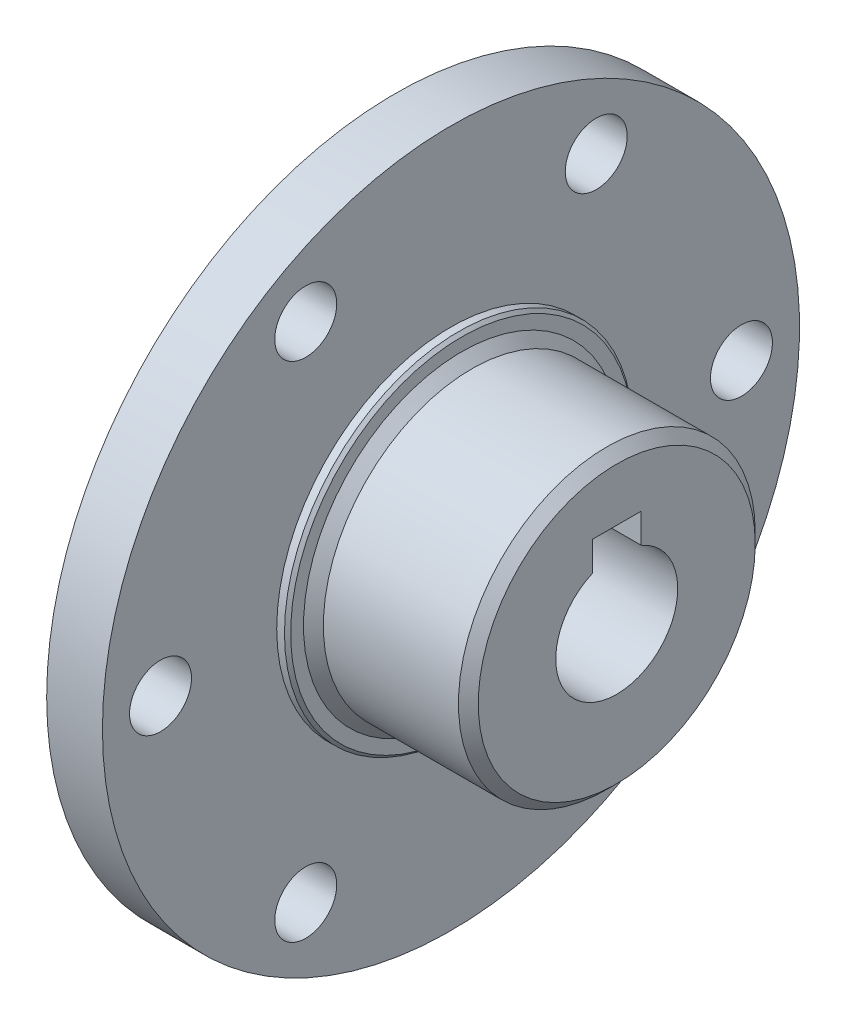
SolidWorks part; units mm, degrees
ref_plane "Front Plane" through (0, 0, 0) normal (0, 0, 1) x (1, 0, 0)
ref_plane "Top Plane" through (0, 0, 0) normal (0, 1, 0) x (1, 0, 0)
ref_plane "Right Plane" through (0, 0, 0) normal (1, 0, 0) x (0, 0, -1)
ref_plane "Plane4" through (0, 0, 0) normal (0, 0, -1) x (-1, 0, 0)
sketch "Sketch1" plane through (0, 0, 0) normal (0, 0, -1) x (-1, 0, 0)
  line L0 (13.0351, 28.575) -> (13.0351, 0)
  line L1 (13.0351, 0) -> (17.6071, 0)
  line L2 (17.6071, 0) -> (17.6071, 28.575)
  line L3 (17.6071, 28.575) -> (13.0351, 28.575)
  line L4 (13.0351, 0) -> (17.6071, 0) construction
revolve "Revolve1" add sketch "Sketch1" angle 360 about L4
sketch "Sketch2" plane through (-13.0351, 0, 0) normal (1, 0, 0) x (0, 0, -1)
  circle A0 centre (0, 0) radius 14.2875
extrude "Boss-Extrude1" add sketch "Sketch2" along normal blind 0.889
sketch "Sketch3" plane through (-12.1461, 0, 0) normal (1, 0, 0) x (0, 0, -1)
  circle A0 centre (0, 0) radius 12.1666
extrude "Boss-Extrude2" add sketch "Sketch3" along normal blind 12.7
sketch "Sketch4" plane through (-17.6071, 0, 0) normal (-1, 0, 0) x (0, 0, 1)
  circle A0 centre (0, 0) radius 14.2875
extrude "Boss-Extrude3" add sketch "Sketch4" along normal blind 0.889
sketch "Sketch5" plane through (-18.4961, 0, 0) normal (-1, 0, 0) x (0, 0, 1)
  line L0 (2, 4.5826) -> (2, 7)
  line L1 (2, 7) -> (-2, 7)
  line L2 (-2, 7) -> (-2, 4.5826)
  arc A0 (-2, 4.5826) -> (2, 4.5826) centre (0, 0) cw
extrude "Cut-Extrude1" cut sketch "Sketch5" against normal through all
sketch "Sketch6" plane through (0, 0, 0) normal (0, 0, -1) x (-1, 0, 0)
  line L0 (-0.5539, 5) -> (-0.5539, 0)
  line L1 (-0.5539, 0) -> (18.4961, 0)
  line L2 (18.4961, 0) -> (18.4961, 5)
  line L3 (18.4961, 5) -> (-0.5539, 5)
  line L4 (-0.5539, 0) -> (18.4961, 0) construction
revolve "Cut-Revolve1" cut sketch "Sketch6" angle 360 about L4
hole_wizard "#10 Clearance Hole1" positions "Sketch8" profile "Sketch7" hole size "#10" standard "ANSI Inch"
sketch "Sketch8" plane through (-17.6071, 0, 0) normal (-1, 0, 0) x (0, 0, 1)
  point P0 (11.9063, 20.6222)
  point P1 (-11.9062, 20.6222)
  point P2 (-23.8125, 0)
  point P3 (-11.9063, -20.6222)
  point P4 (11.9062, -20.6222)
  point P5 (23.8125, 0)
sketch "Sketch7" plane through (-17.6071, 20.6222, 11.9063) normal (0, 1, 0) x (0, 0, 1)
  line L0 (0, 0) -> (0, 18.161)
  line L1 (0, 18.161) -> (2.54, 18.161)
  line L2 (2.54, 18.161) -> (2.54, 0)
  line L5 (2.54, 0) -> (0, 0)
  line L11 (0, -6.35) -> (0, 107.95) construction
  dimension "Thru Hole Dia." = 5.08
  dimension "Thru Hole Depth" = 18.161
chamfer "Chamfer1" distance 0.254 angle 45 2 edges at (-12.1461, 0, -14.2875) (-18.4961, 0, 14.2875)
chamfer "Chamfer2" distance 0.8128 angle 45 2 edges at (-12.1461, 0, -12.1666) (0.5539, 0, -12.1666)
